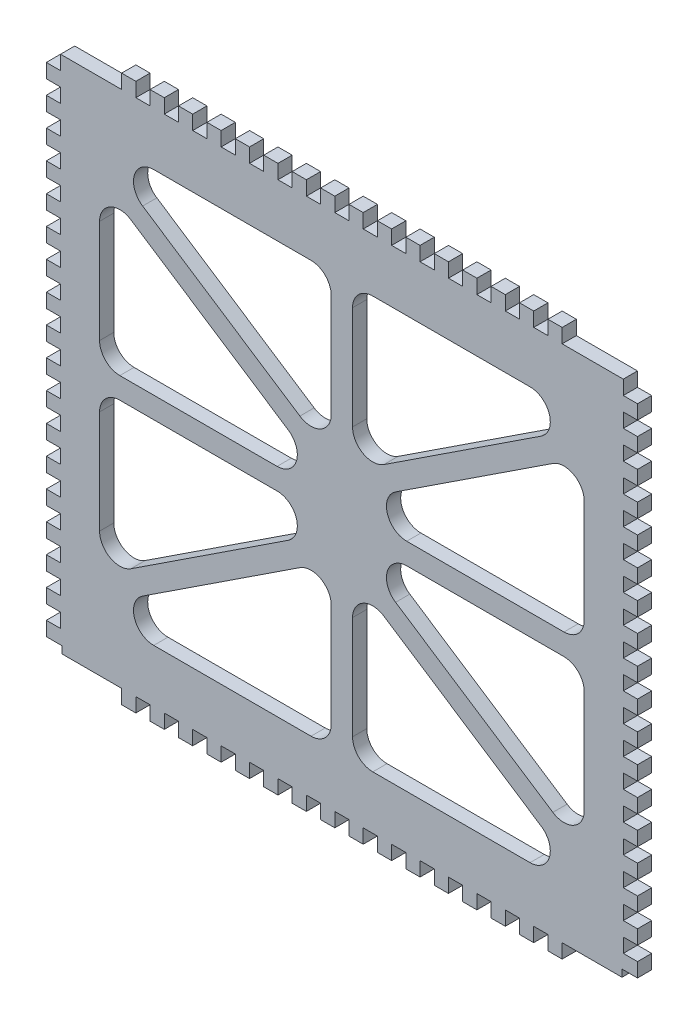
SolidWorks part; units mm, degrees
material "Cedar"
ref_plane "Front Plane" through (0, 0, 0) normal (0, 0, 1) x (1, 0, 0)
ref_plane "Top Plane" through (0, 0, 0) normal (0, 1, 0) x (1, 0, 0)
ref_plane "Right Plane" through (0, 0, 0) normal (1, 0, 0) x (0, 0, -1)
sketch "Sketch1" plane through (0, 0, 0) normal (0, 0, 1) x (1, 0, 0)
  line L0 (0, 0) -> (0, 50) construction
  line L2 (-83.21, -73) -> (-83.21, 73)
  line L3 (-83.21, 73) -> (83.21, 73)
  line L5 (-52.9664, 58) -> (-8.697, 58)
  line L6 (-28.4052, 22.1841) -> (-25.1122, 27.1996) construction
  line L7 (83.21, -73) -> (83.21, 73)
  line L8 (-83.21, -73) -> (83.21, -73)
  line L9 (-26.7587, 24.6918) -> (-13.0043, 15.6612) construction
  line L10 (-56.0931, 47.5406) -> (-11.8238, 18.4749)
  line L11 (-3, 23.2372) -> (-3, 52.303)
  line L12 (-59.3862, 42.5251) -> (-15.1169, 13.4594)
  line L13 (-18.2436, 3) -> (-62.513, 3)
  line L14 (57.7397, 45.0329) -> (56.0931, 47.5406) construction
  line L15 (59.3862, 42.5251) -> (57.7397, 45.0329) construction
  line L16 (49.9964, 39.9489) -> (64.903, 49.7361) construction
  line L17 (51.6429, 37.4411) -> (48.3499, 42.4567) construction
  line L18 (15.1169, 13.4594) -> (13.4703, 15.9671) construction
  line L19 (-11.8238, 18.4749) -> (-13.4703, 15.9671) construction
  line L20 (-15.1169, 13.4594) -> (-13.4703, 15.9671) construction
  line L21 (-51.6429, 37.4411) -> (-48.3499, 42.4567) construction
  line L22 (-49.9964, 39.9489) -> (-64.903, 49.7361) construction
  line L23 (-59.3862, 42.5251) -> (-57.7397, 45.0329) construction
  line L24 (-57.7397, 45.0329) -> (-56.0931, 47.5406) construction
  line L25 (11.8238, 18.4749) -> (13.4703, 15.9671) construction
  line L26 (26.7587, 24.6918) -> (13.0043, 15.6612) construction
  line L27 (28.4052, 22.1841) -> (25.1122, 27.1996) construction
  line L28 (-68.21, 8.697) -> (-68.21, 37.7628)
  line L29 (68.21, 8.697) -> (68.21, 37.7628)
  line L30 (18.2436, 3) -> (62.513, 3)
  line L31 (-83.21, 73) -> (-83.21, -73) construction
  line L32 (-83.21, 0) -> (-72.8381, 0) construction
  line L33 (59.3862, 42.5251) -> (15.1169, 13.4594)
  line L34 (3, 23.2372) -> (3, 52.303)
  line L35 (56.0931, 47.5406) -> (11.8238, 18.4749)
  line L36 (52.9664, 58) -> (8.697, 58)
  line L37 (28.4052, -22.1841) -> (25.1122, -27.1996) construction
  line L38 (26.7587, -24.6918) -> (13.0043, -15.6612) construction
  line L39 (11.8238, -18.4749) -> (13.4703, -15.9671) construction
  line L40 (-57.7397, -45.0329) -> (-56.0931, -47.5406) construction
  line L41 (-59.3862, -42.5251) -> (-57.7397, -45.0329) construction
  line L42 (-49.9964, -39.9489) -> (-64.903, -49.7361) construction
  line L43 (-51.6429, -37.4411) -> (-48.3499, -42.4567) construction
  line L44 (-15.1169, -13.4594) -> (-13.4703, -15.9671) construction
  line L45 (-11.8238, -18.4749) -> (-13.4703, -15.9671) construction
  line L46 (15.1169, -13.4594) -> (13.4703, -15.9671) construction
  line L47 (51.6429, -37.4411) -> (48.3499, -42.4567) construction
  line L48 (49.9964, -39.9489) -> (64.903, -49.7361) construction
  line L49 (59.3862, -42.5251) -> (57.7397, -45.0329) construction
  line L50 (57.7397, -45.0329) -> (56.0931, -47.5406) construction
  line L51 (-26.7587, -24.6918) -> (-13.0043, -15.6612) construction
  line L52 (-28.4052, -22.1841) -> (-25.1122, -27.1996) construction
  line L53 (52.9664, -58) -> (8.697, -58)
  line L54 (56.0931, -47.5406) -> (11.8238, -18.4749)
  line L55 (3, -23.2372) -> (3, -52.303)
  line L56 (59.3862, -42.5251) -> (15.1169, -13.4594)
  line L57 (18.2436, -3) -> (62.513, -3)
  line L58 (68.21, -8.697) -> (68.21, -37.7628)
  line L59 (-68.21, -8.697) -> (-68.21, -37.7628)
  line L60 (-18.2436, -3) -> (-62.513, -3)
  line L61 (-59.3862, -42.5251) -> (-15.1169, -13.4594)
  line L62 (-3, -23.2372) -> (-3, -52.303)
  line L63 (-56.0931, -47.5406) -> (-11.8238, -18.4749)
  line L64 (-52.9664, -58) -> (-8.697, -58)
  arc A0 (68.21, 37.7628) -> (59.3862, 42.5251) centre (62.513, 37.7628) ccw
  arc A1 (68.21, 8.697) -> (62.513, 3) centre (62.513, 8.697) cw
  arc A2 (15.1169, 13.4594) -> (18.2436, 3) centre (18.2436, 8.697) ccw
  arc A3 (3, 23.2372) -> (11.8238, 18.4749) centre (8.697, 23.2372) ccw
  arc A4 (3, 52.303) -> (8.697, 58) centre (8.697, 52.303) cw
  arc A5 (56.0931, 47.5406) -> (52.9664, 58) centre (52.9664, 52.303) ccw
  arc A6 (-56.0931, 47.5406) -> (-52.9664, 58) centre (-52.9664, 52.303) cw
  arc A7 (-3, 52.303) -> (-8.697, 58) centre (-8.697, 52.303) ccw
  arc A8 (-3, 23.2372) -> (-11.8238, 18.4749) centre (-8.697, 23.2372) cw
  arc A9 (-15.1169, 13.4594) -> (-18.2436, 3) centre (-18.2436, 8.697) cw
  arc A10 (-68.21, 8.697) -> (-62.513, 3) centre (-62.513, 8.697) ccw
  arc A11 (-68.21, 37.7628) -> (-59.3862, 42.5251) centre (-62.513, 37.7628) cw
  arc A12 (-68.21, -37.7628) -> (-59.3862, -42.5251) centre (-62.513, -37.7628) ccw
  arc A13 (-68.21, -8.697) -> (-62.513, -3) centre (-62.513, -8.697) cw
  arc A14 (-15.1169, -13.4594) -> (-18.2436, -3) centre (-18.2436, -8.697) ccw
  arc A15 (-3, -23.2372) -> (-11.8238, -18.4749) centre (-8.697, -23.2372) ccw
  arc A16 (-3, -52.303) -> (-8.697, -58) centre (-8.697, -52.303) cw
  arc A17 (-56.0931, -47.5406) -> (-52.9664, -58) centre (-52.9664, -52.303) ccw
  arc A18 (56.0931, -47.5406) -> (52.9664, -58) centre (52.9664, -52.303) cw
  arc A19 (3, -52.303) -> (8.697, -58) centre (8.697, -52.303) ccw
  arc A20 (3, -23.2372) -> (11.8238, -18.4749) centre (8.697, -23.2372) cw
  arc A21 (15.1169, -13.4594) -> (18.2436, -3) centre (18.2436, -8.697) cw
  arc A22 (68.21, -8.697) -> (62.513, -3) centre (62.513, -8.697) ccw
  arc A23 (68.21, -37.7628) -> (59.3862, -42.5251) centre (62.513, -37.7628) cw
  point P19 (0, 58)
  point P21 (0, 73)
  point P27 (-64, 0)
  point P34 (-63.85, 0)
  point P47 (-72.0236, 58)
  point P52 (-3, 12.6815)
  point P59 (-54.2157, 58)
  point P73 (54.2157, 58)
  point P74 (3, 12.6815)
  point P75 (72.0236, 58)
  point P132 (72.0236, -58)
  point P133 (3, -12.6815)
  point P134 (54.2157, -58)
  point P135 (-54.2157, -58)
  point P136 (-3, -12.6815)
  point P137 (-72.0236, -58)
  point P138 (0, -58)
  dimension "D3" = 15
  dimension "D8" = 146
  dimension "D10" = 3
  dimension "D11" = 3
  dimension "D2" = 166.42
  dimension "D4" = 15
  dimension "D5" = 6
extrude "Boss-Extrude1" add sketch "Sketch1" along normal blind 4
sketch "Sketch2" plane through (0, 0, 4) normal (0, 0, 1) x (1, 0, 0)
  line L0 (0, 0) -> (-89.2695, 0) construction
  line L1 (0, 0) -> (0, 71.1996) construction
  line L2 (-83.21, -73) -> (83.21, -73) construction
  line L3 (-83.21, -71) -> (-78.85, -71)
  line L4 (-83.21, -71) -> (-83.21, -73)
  line L5 (-83.21, 61) -> (-79.21, 61)
  line L6 (-83.21, 61) -> (-83.21, 65)
  line L7 (-83.21, 65) -> (-79.21, 65)
  line L8 (-79.21, 61) -> (-79.21, 65)
  line L9 (-83.21, 53) -> (-79.21, 53)
  line L10 (-83.21, 53) -> (-83.21, 57)
  line L11 (-83.21, 57) -> (-79.21, 57)
  line L12 (-79.21, 53) -> (-79.21, 57)
  line L13 (-83.21, 45) -> (-79.21, 45)
  line L14 (-83.21, 45) -> (-83.21, 49)
  line L15 (-83.21, 49) -> (-79.21, 49)
  line L16 (-79.21, 45) -> (-79.21, 49)
  line L17 (-83.21, 37) -> (-79.21, 37)
  line L18 (-83.21, 37) -> (-83.21, 41)
  line L19 (-83.21, 41) -> (-79.21, 41)
  line L20 (-79.21, 37) -> (-79.21, 41)
  line L21 (-83.21, 29) -> (-79.21, 29)
  line L22 (-83.21, 29) -> (-83.21, 33)
  line L23 (-83.21, 33) -> (-79.21, 33)
  line L24 (-79.21, 29) -> (-79.21, 33)
  line L25 (-83.21, 21) -> (-79.21, 21)
  line L26 (-83.21, 21) -> (-83.21, 25)
  line L27 (-83.21, 25) -> (-79.21, 25)
  line L28 (-79.21, 21) -> (-79.21, 25)
  line L29 (-83.21, 13) -> (-79.21, 13)
  line L30 (-83.21, 13) -> (-83.21, 17)
  line L31 (-83.21, 17) -> (-79.21, 17)
  line L32 (-79.21, 13) -> (-79.21, 17)
  line L33 (-83.21, 5) -> (-79.21, 5)
  line L34 (-83.21, 5) -> (-83.21, 9)
  line L35 (-83.21, 9) -> (-79.21, 9)
  line L36 (-79.21, 5) -> (-79.21, 9)
  line L37 (-83.21, -3) -> (-79.21, -3)
  line L38 (-83.21, -3) -> (-83.21, 1)
  line L39 (-83.21, 1) -> (-79.21, 1)
  line L40 (-79.21, -3) -> (-79.21, 1)
  line L41 (-83.21, -11) -> (-79.21, -11)
  line L42 (-83.21, -11) -> (-83.21, -7)
  line L43 (-83.21, -7) -> (-79.21, -7)
  line L44 (-79.21, -11) -> (-79.21, -7)
  line L45 (-83.21, -19) -> (-79.21, -19)
  line L46 (-83.21, -19) -> (-83.21, -15)
  line L47 (-83.21, -15) -> (-79.21, -15)
  line L48 (-79.21, -19) -> (-79.21, -15)
  line L49 (-83.21, -27) -> (-79.21, -27)
  line L50 (-83.21, -27) -> (-83.21, -23)
  line L51 (-83.21, -23) -> (-79.21, -23)
  line L52 (-79.21, -27) -> (-79.21, -23)
  line L53 (-83.21, -35) -> (-79.21, -35)
  line L54 (-83.21, -35) -> (-83.21, -31)
  line L55 (-83.21, -31) -> (-79.21, -31)
  line L56 (-79.21, -35) -> (-79.21, -31)
  line L57 (-83.21, -73) -> (-83.21, 73) construction
  line L58 (-83.21, -43) -> (-79.21, -43)
  line L59 (-83.21, -43) -> (-83.21, -39)
  line L60 (79.21, -67) -> (79.21, -63)
  line L61 (83.21, -63) -> (79.21, -63)
  line L62 (83.21, -67) -> (83.21, -63)
  line L63 (83.21, -67) -> (79.21, -67)
  line L64 (-83.21, -39) -> (-79.21, -39)
  line L65 (-79.21, -43) -> (-79.21, -39)
  line L66 (-83.21, -51) -> (-79.21, -51)
  line L67 (79.21, -59) -> (79.21, -55)
  line L68 (83.21, -55) -> (79.21, -55)
  line L69 (83.21, -59) -> (83.21, -55)
  line L70 (83.21, -59) -> (79.21, -59)
  line L71 (79.21, -51) -> (79.21, -47)
  line L72 (83.21, -47) -> (79.21, -47)
  line L73 (83.21, -51) -> (83.21, -47)
  line L74 (79.21, 69) -> (79.21, 73)
  line L75 (83.21, 73) -> (79.21, 73)
  line L76 (83.21, 69) -> (83.21, 73)
  line L77 (83.21, 69) -> (79.21, 69)
  line L78 (83.21, -51) -> (79.21, -51)
  line L79 (79.21, -43) -> (79.21, -39)
  line L80 (83.21, -39) -> (79.21, -39)
  line L81 (83.21, -43) -> (83.21, -39)
  line L82 (83.21, -43) -> (79.21, -43)
  line L83 (79.21, -35) -> (79.21, -31)
  line L84 (83.21, -31) -> (79.21, -31)
  line L85 (83.21, -35) -> (83.21, -31)
  line L86 (83.21, -35) -> (79.21, -35)
  line L87 (79.21, -27) -> (79.21, -23)
  line L88 (83.21, -23) -> (79.21, -23)
  line L89 (83.21, -27) -> (83.21, -23)
  line L90 (83.21, -27) -> (79.21, -27)
  line L91 (79.21, -19) -> (79.21, -15)
  line L92 (83.21, -15) -> (79.21, -15)
  line L93 (83.21, -19) -> (83.21, -15)
  line L94 (83.21, -19) -> (79.21, -19)
  line L95 (79.21, -11) -> (79.21, -7)
  line L96 (83.21, -7) -> (79.21, -7)
  line L97 (83.21, -11) -> (83.21, -7)
  line L98 (83.21, -11) -> (79.21, -11)
  line L99 (79.21, -3) -> (79.21, 1)
  line L100 (83.21, 1) -> (79.21, 1)
  line L101 (83.21, -3) -> (83.21, 1)
  line L102 (83.21, -3) -> (79.21, -3)
  line L103 (-83.21, 69) -> (-79.21, 69)
  line L104 (-83.21, 69) -> (-83.21, 73)
  line L105 (-83.21, 73) -> (-79.21, 73)
  line L106 (-79.21, 69) -> (-79.21, 73)
  line L107 (79.21, 5) -> (79.21, 9)
  line L108 (83.21, 9) -> (79.21, 9)
  line L109 (83.21, 5) -> (83.21, 9)
  line L110 (83.21, 5) -> (79.21, 5)
  line L111 (79.21, 13) -> (79.21, 17)
  line L112 (83.21, 17) -> (79.21, 17)
  line L113 (83.21, 13) -> (83.21, 17)
  line L114 (83.21, 13) -> (79.21, 13)
  line L115 (79.21, 21) -> (79.21, 25)
  line L116 (83.21, 25) -> (79.21, 25)
  line L117 (83.21, 21) -> (83.21, 25)
  line L118 (83.21, 21) -> (79.21, 21)
  line L119 (79.21, 29) -> (79.21, 33)
  line L120 (83.21, 33) -> (79.21, 33)
  line L121 (83.21, 29) -> (83.21, 33)
  line L122 (83.21, 29) -> (79.21, 29)
  line L123 (-83.21, -51) -> (-83.21, -47)
  line L124 (-83.21, -47) -> (-79.21, -47)
  line L125 (-79.21, -51) -> (-79.21, -47)
  line L126 (79.21, 37) -> (79.21, 41)
  line L127 (83.21, 41) -> (79.21, 41)
  line L128 (83.21, 37) -> (83.21, 41)
  line L129 (83.21, 37) -> (79.21, 37)
  line L130 (79.21, 45) -> (79.21, 49)
  line L131 (83.21, 49) -> (79.21, 49)
  line L132 (83.21, 45) -> (83.21, 49)
  line L133 (83.21, 45) -> (79.21, 45)
  line L134 (-83.21, 73) -> (83.21, 73) construction
  line L135 (-83.21, -59) -> (-79.21, -59)
  line L136 (-83.21, -59) -> (-83.21, -55)
  line L137 (-83.21, -55) -> (-79.21, -55)
  line L138 (-79.21, -59) -> (-79.21, -55)
  line L139 (-83.21, -67) -> (-79.21, -67)
  line L140 (-83.21, -67) -> (-83.21, -63)
  line L141 (-83.21, -63) -> (-79.21, -63)
  line L142 (-79.21, -67) -> (-79.21, -63)
  line L143 (79.21, 53) -> (79.21, 57)
  line L144 (83.21, 57) -> (79.21, 57)
  line L145 (83.21, 53) -> (83.21, 57)
  line L146 (83.21, 53) -> (79.21, 53)
  line L147 (79.21, 61) -> (79.21, 65)
  line L148 (83.21, 65) -> (79.21, 65)
  line L149 (83.21, 61) -> (83.21, 65)
  line L150 (83.21, 61) -> (79.21, 61)
  line L151 (-83.21, -73) -> (-78.85, -73)
  line L152 (-78.85, -71) -> (-78.85, -73)
  line L154 (83.21, -73) -> (78.85, -73)
  line L155 (83.21, -73) -> (83.21, -71)
  line L156 (83.21, -71) -> (78.85, -71)
  line L157 (78.85, -73) -> (78.85, -71)
  dimension "D1" = 4
  dimension "D2" = 4
  dimension "D3" = 4
  dimension "D4" = 18
  dimension "D5" = 4
extrude "Cut-Extrude1" cut sketch "Sketch2" against normal blind 4
sketch "Sketch3" plane through (0, 0, 4) normal (0, 0, 1) x (1, 0, 0)
  line L0 (0, 73) -> (0, 90.0884) construction
  line L1 (0, 0) -> (-53.0155, 0) construction
  line L2 (-83.21, 73) -> (83.21, 73) construction
  line L3 (-2, 73) -> (-6, 73)
  line L4 (-2, 73) -> (-2, 77)
  line L5 (-2, 77) -> (-6, 77)
  line L6 (-6, 73) -> (-6, 77)
  line L7 (-10, 73) -> (-14, 73)
  line L8 (-10, 73) -> (-10, 77)
  line L9 (-10, 77) -> (-14, 77)
  line L10 (-14, 73) -> (-14, 77)
  line L11 (-18, 73) -> (-22, 73)
  line L12 (-18, 73) -> (-18, 77)
  line L13 (-18, 77) -> (-22, 77)
  line L14 (-22, 73) -> (-22, 77)
  line L15 (-26, 73) -> (-30, 73)
  line L16 (-26, 73) -> (-26, 77)
  line L17 (-26, 77) -> (-30, 77)
  line L18 (-30, 73) -> (-30, 77)
  line L19 (-34, 73) -> (-38, 73)
  line L20 (-34, 73) -> (-34, 77)
  line L21 (-34, 77) -> (-38, 77)
  line L22 (-38, 73) -> (-38, 77)
  line L23 (-42, 73) -> (-46, 73)
  line L24 (-42, 73) -> (-42, 77)
  line L25 (-42, 77) -> (-46, 77)
  line L26 (-46, 73) -> (-46, 77)
  line L27 (-50, 73) -> (-54, 73)
  line L28 (-50, 73) -> (-50, 77)
  line L29 (-50, 77) -> (-54, 77)
  line L30 (-54, 73) -> (-54, 77)
  line L31 (-58, 73) -> (-62, 73)
  line L32 (-58, 73) -> (-58, 77)
  line L33 (-58, 77) -> (-62, 77)
  line L34 (-62, 73) -> (-62, 77)
  line L35 (62, 73) -> (62, 77)
  line L36 (58, 77) -> (62, 77)
  line L37 (58, 73) -> (58, 77)
  line L38 (58, 73) -> (62, 73)
  line L39 (54, 73) -> (54, 77)
  line L40 (50, 77) -> (54, 77)
  line L41 (50, 73) -> (50, 77)
  line L42 (50, 73) -> (54, 73)
  line L43 (46, 73) -> (46, 77)
  line L44 (42, 77) -> (46, 77)
  line L45 (42, 73) -> (42, 77)
  line L46 (42, 73) -> (46, 73)
  line L47 (38, 73) -> (38, 77)
  line L48 (34, 77) -> (38, 77)
  line L49 (34, 73) -> (34, 77)
  line L50 (34, 73) -> (38, 73)
  line L51 (30, 73) -> (30, 77)
  line L52 (26, 77) -> (30, 77)
  line L53 (26, 73) -> (26, 77)
  line L54 (26, 73) -> (30, 73)
  line L55 (22, 73) -> (22, 77)
  line L56 (18, 77) -> (22, 77)
  line L57 (18, 73) -> (18, 77)
  line L58 (18, 73) -> (22, 73)
  line L59 (14, 73) -> (14, 77)
  line L60 (10, 77) -> (14, 77)
  line L61 (10, 73) -> (10, 77)
  line L62 (10, 73) -> (14, 73)
  line L63 (6, 73) -> (6, 77)
  line L64 (2, 77) -> (6, 77)
  line L65 (2, 73) -> (2, 77)
  line L66 (2, 73) -> (6, 73)
  line L67 (2, -73) -> (6, -73)
  line L68 (2, -73) -> (2, -77)
  line L69 (2, -77) -> (6, -77)
  line L70 (6, -73) -> (6, -77)
  line L71 (10, -73) -> (14, -73)
  line L72 (10, -73) -> (10, -77)
  line L73 (10, -77) -> (14, -77)
  line L74 (14, -73) -> (14, -77)
  line L75 (18, -73) -> (22, -73)
  line L76 (18, -73) -> (18, -77)
  line L77 (18, -77) -> (22, -77)
  line L78 (22, -73) -> (22, -77)
  line L79 (26, -73) -> (30, -73)
  line L80 (26, -73) -> (26, -77)
  line L81 (26, -77) -> (30, -77)
  line L82 (30, -73) -> (30, -77)
  line L83 (34, -73) -> (38, -73)
  line L84 (34, -73) -> (34, -77)
  line L85 (34, -77) -> (38, -77)
  line L86 (38, -73) -> (38, -77)
  line L87 (42, -73) -> (46, -73)
  line L88 (42, -73) -> (42, -77)
  line L89 (42, -77) -> (46, -77)
  line L90 (46, -73) -> (46, -77)
  line L91 (50, -73) -> (54, -73)
  line L92 (50, -73) -> (50, -77)
  line L93 (50, -77) -> (54, -77)
  line L94 (54, -73) -> (54, -77)
  line L95 (58, -73) -> (62, -73)
  line L96 (58, -73) -> (58, -77)
  line L97 (58, -77) -> (62, -77)
  line L98 (62, -73) -> (62, -77)
  line L99 (-62, -73) -> (-62, -77)
  line L100 (-58, -77) -> (-62, -77)
  line L101 (-58, -73) -> (-58, -77)
  line L102 (-58, -73) -> (-62, -73)
  line L103 (-54, -73) -> (-54, -77)
  line L104 (-50, -77) -> (-54, -77)
  line L105 (-50, -73) -> (-50, -77)
  line L106 (-50, -73) -> (-54, -73)
  line L107 (-46, -73) -> (-46, -77)
  line L108 (-42, -77) -> (-46, -77)
  line L109 (-42, -73) -> (-42, -77)
  line L110 (-42, -73) -> (-46, -73)
  line L111 (-38, -73) -> (-38, -77)
  line L112 (-34, -77) -> (-38, -77)
  line L113 (-34, -73) -> (-34, -77)
  line L114 (-34, -73) -> (-38, -73)
  line L115 (-30, -73) -> (-30, -77)
  line L116 (-26, -77) -> (-30, -77)
  line L117 (-26, -73) -> (-26, -77)
  line L118 (-26, -73) -> (-30, -73)
  line L119 (-22, -73) -> (-22, -77)
  line L120 (-18, -77) -> (-22, -77)
  line L121 (-18, -73) -> (-18, -77)
  line L122 (-18, -73) -> (-22, -73)
  line L123 (-14, -73) -> (-14, -77)
  line L124 (-10, -77) -> (-14, -77)
  line L125 (-10, -73) -> (-10, -77)
  line L126 (-10, -73) -> (-14, -73)
  line L127 (-6, -73) -> (-6, -77)
  line L128 (-2, -77) -> (-6, -77)
  line L129 (-2, -73) -> (-2, -77)
  line L130 (-2, -73) -> (-6, -73)
  dimension "D1" = 4
  dimension "D2" = 2
  dimension "D3" = 4
  dimension "D4" = 8
extrude "Boss-Extrude2" add sketch "Sketch3" against normal blind 4
